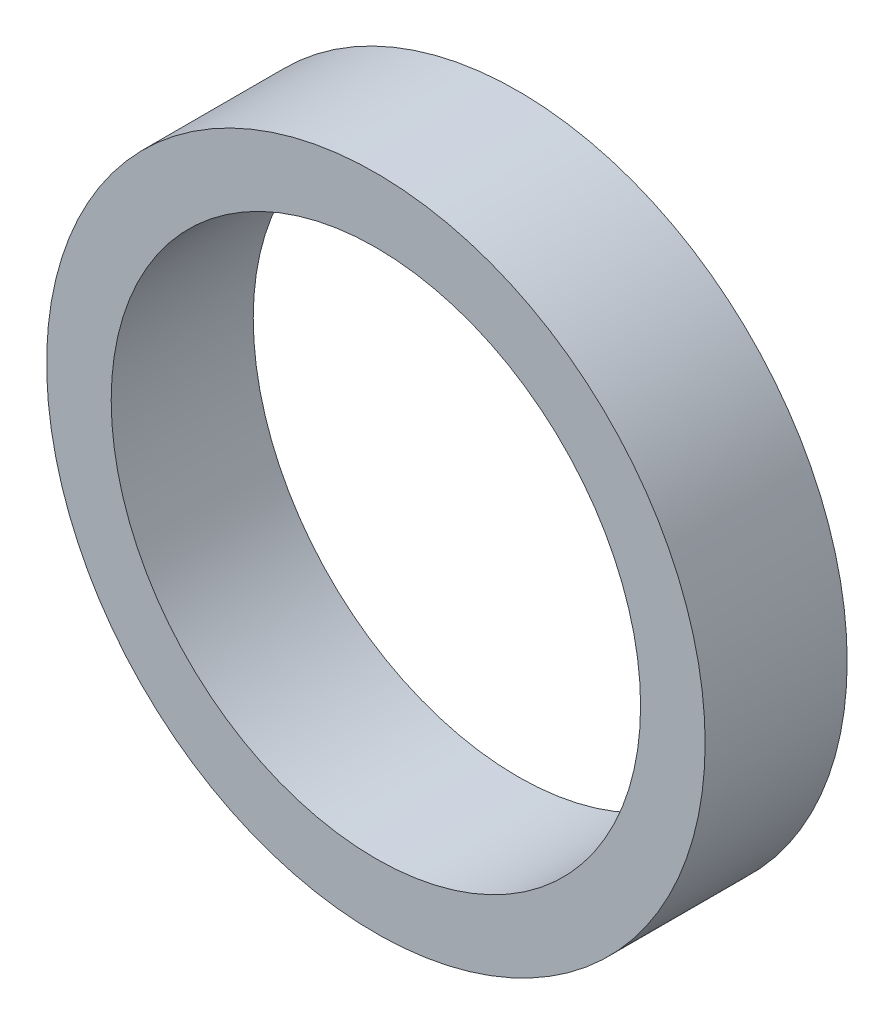
SolidWorks part; units mm, degrees
ref_plane "Front" through (0, 0, 0) normal (0, 0, 1) x (1, 0, 0)
ref_plane "Top" through (0, 0, 0) normal (0, 1, 0) x (1, 0, 0)
ref_plane "Right" through (0, 0, 0) normal (1, 0, 0) x (0, 0, -1)
sketch "Sketch1" plane through (0, 0, 0) normal (0, 0, 1) x (1, 0, 0)
  circle A0 centre (0, 0) radius 25.5
  circle A1 centre (0, 0) radius 20.5
  dimension "D1" = 51
  dimension "D2" = 5
extrude "Boss-Extrude1" add sketch "Sketch1" along normal blind 11
